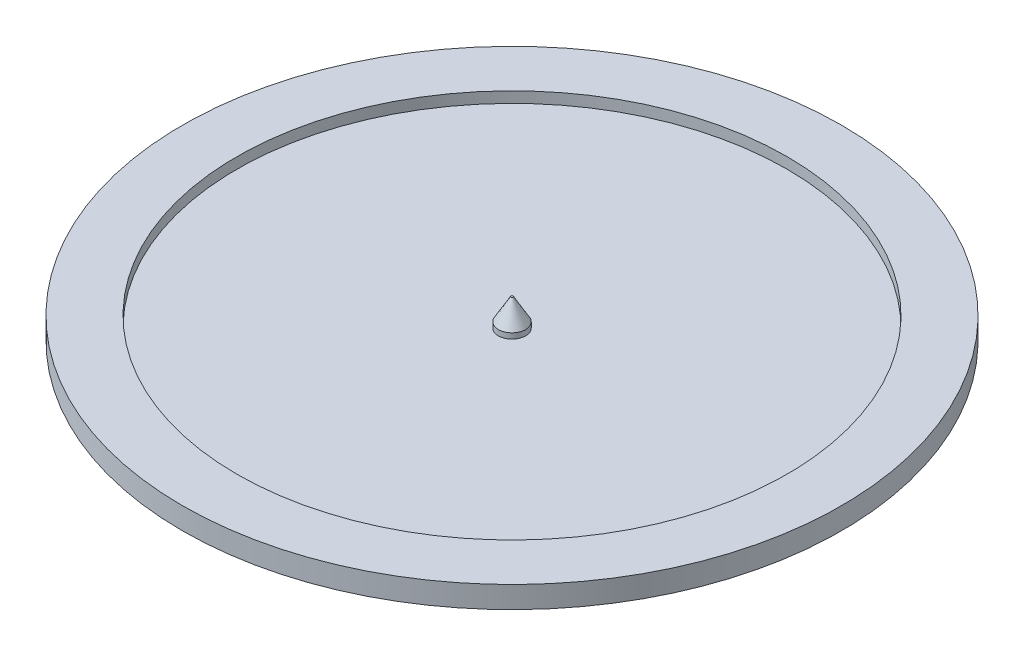
SolidWorks part; units mm, degrees
ref_plane "Front Plane" through (0, 0, 0) normal (0, 0, 1) x (1, 0, 0)
ref_plane "Top Plane" through (0, 0, 0) normal (0, 1, 0) x (1, 0, 0)
ref_plane "Right Plane" through (0, 0, 0) normal (1, 0, 0) x (0, 0, -1)
sketch "Sketch1" plane through (0, 0, 0) normal (0, 1, 0) x (1, 0, 0)
  circle A2 centre (0, 0) radius 60.5
  dimension "D1" = 121
extrude "Boss-Extrude1" add sketch "Sketch1" along normal blind 2
sketch "Sketch2" plane through (0, 2, 0) normal (0, 1, 0) x (1, 0, 0)
  circle A3 centre (0, 0) radius 60.5 construction
  circle A4 centre (0, 0) radius 60.5
  circle A5 centre (0, 0) radius 50.5
  dimension "D1" = 10
extrude "Boss-Extrude3" add sketch "Sketch2" along normal blind 2
sketch "Sketch3" plane through (0, 2, 0) normal (0, 1, 0) x (1, 0, 0)
  circle A0 centre (0, 0) radius 2.5
  dimension "D1" = 5
extrude "Boss-Extrude4" add sketch "Sketch3" along normal blind 5
chamfer "Chamfer1" distance 4 angle 30 1 edges at (0, 7, 2.5)
